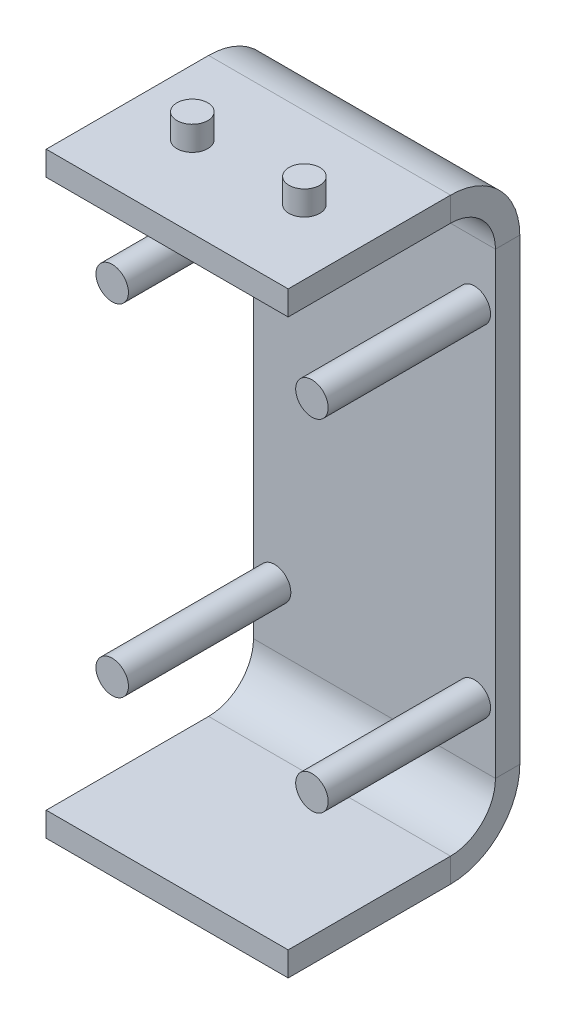
SolidWorks part; units mm, degrees
ref_plane "前视基准面" through (0, 0, 0) normal (0, 0, 1) x (1, 0, 0)
ref_plane "上视基准面" through (0, 0, 0) normal (0, 1, 0) x (1, 0, 0)
ref_plane "右视基准面" through (0, 0, 0) normal (1, 0, 0) x (0, 0, -1)
sketch "草图1" plane through (0, 0, 0) normal (0, 0, 1) x (1, 0, 0)
  line L1 (-7.45, -0.75) -> (7.45, -0.75)
  line L2 (-7.45, -0.75) -> (-7.45, 0.75)
  line L3 (-7.45, 0.75) -> (7.45, 0.75)
  line L4 (7.45, -0.75) -> (7.45, 0.75)
  line L5 (-7.45, -0.75) -> (7.45, 0.75) construction
  line L6 (-7.45, 0.75) -> (7.45, -0.75) construction
  point P0 (0, 0)
  dimension "D1" = 1.5
  dimension "D2" = 14.9
sketch "草图6" plane through (0, 0, 0) normal (1, 0, 0) x (0, 0, -1)
  line L0 (0, 0) -> (10, 0)
  line L1 (0, -0.75) -> (0, 0.75) construction
  line L2 (13.5136, -3.5136) -> (13.5136, -31.7364)
  line L3 (0, -35.25) -> (10, -35.25)
  line L4 (0, 0) -> (0, -35.25) construction
  line L5 (0, -17.625) -> (17.978, -17.625) construction
  arc A0 (10, 0) -> (13.5136, -3.5136) centre (10, -3.5136) cw
  arc A1 (13.5136, -31.7364) -> (10, -35.25) centre (10, -31.7364) cw
  dimension "D1" = 10
  dimension "D2" = 35.25
  dimension "D3" = 28.2227
sweep "扫描5" add profiles "草图1" path "草图6"
sketch "草图8" plane through (0, 0, 0) normal (0, 1, 0) x (1, 0, 0)
  line L0 (-7.45, 10) -> (-7.45, 0) construction
  line L1 (7.45, 0) -> (-7.45, 0) construction
  circle A0 centre (-3.45, 5) radius 0.95
  circle A1 centre (3.45, 5) radius 0.95
  dimension "D1" = 1.9
  dimension "D2" = 1.9
  dimension "D3" = 4
  dimension "D5" = 5
  dimension "D4" = 6.9
extrude "凸台-拉伸1" add sketch "草图8" along normal blind 1.5 from surface at 0.75 separate body contours A0 | A1 starting at face at (0, 0.75, -5)
sketch "草图10" plane through (0, -34.5, 0) normal (0, 1, 0) x (1, 0, 0)
  line L4 (7.45, 10) -> (-7.45, 10)
  line L5 (-7.45, 10) -> (-7.45, 0)
  line L6 (-7.45, 0) -> (7.45, 0)
  line L7 (7.45, 0) -> (7.45, 10)
  line L8 (7.45, 10) -> (-7.45, 10)
  line L9 (-7.45, 10) -> (-7.45, 0)
  line L10 (-7.45, 0) -> (7.45, 0)
  line L11 (7.45, 0) -> (7.45, 10)
  circle A0 centre (3.45, 5) radius 0.95 construction
  circle A1 centre (-3.45, 5) radius 0.95 construction
  circle A2 centre (3.45, 5) radius 0.95
  circle A3 centre (-3.45, 5) radius 0.95
  dimension "D1" = 0
extrude "凸台-拉伸2" add sketch "草图10" against normal blind 1.5 from surface at -1.5 contours A3 | A2 starting at face at (0, -36, -5)
ref_plane "基准面1" through (0, 0, -12.7636) normal (0, 0, 1) x (1, 0, 0)
sketch "草图12" plane through (0, 0, -12.7636) normal (0, 0, 1) x (1, 0, 0)
  line L0 (-7.45, -3.5136) -> (7.45, -3.5136) construction
  line L1 (0, -3.5136) -> (0, -31.7364) construction
  line L2 (-7.45, -31.7364) -> (7.45, -31.7364) construction
  line L3 (0, -17.625) -> (12.9516, -17.625) construction
  circle A0 centre (-6.15, -28.125) radius 1
  circle A1 centre (-6.15, -7.125) radius 1
  circle A2 centre (6.15, -7.125) radius 1
  circle A3 centre (6.15, -28.125) radius 1
  point P10 (-45.0018, -12.09)
  point P11 (-43.8532, -11.9333)
  dimension "D3" = 2
  dimension "D4" = 2
  dimension "D5" = 12.3
  dimension "D6" = 21
extrude "凸台-拉伸3" add sketch "草图12" along normal blind 10
